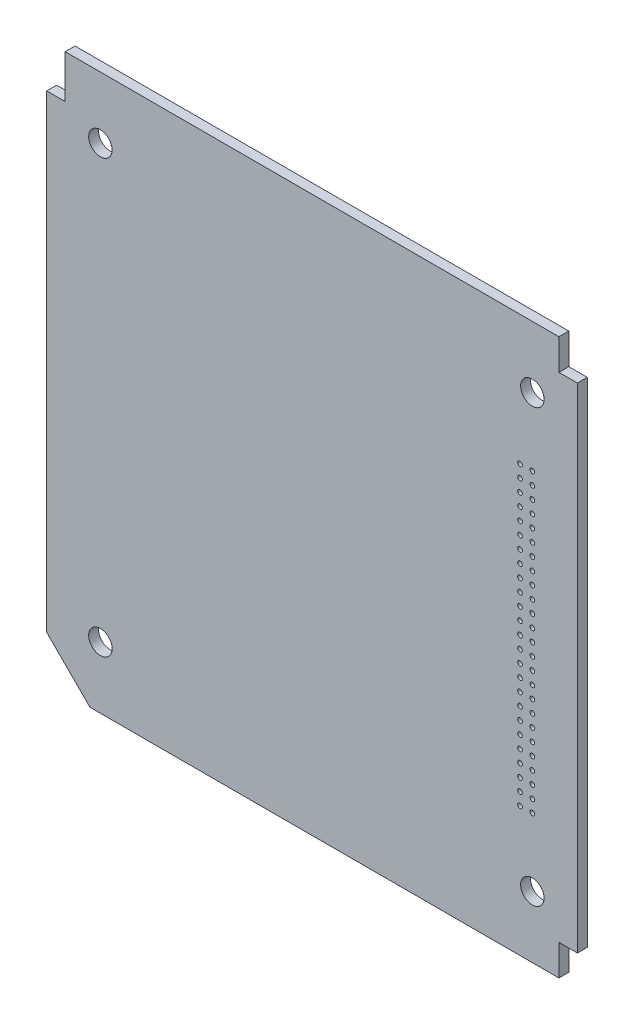
SolidWorks part; units mm, degrees
material "電力回路基板"
ref_plane "正面" through (0, 0, 0) normal (0, 0, 1) x (1, 0, 0)
ref_plane "平面" through (0, 0, 0) normal (0, 1, 0) x (1, 0, 0)
ref_plane "右側面" through (0, 0, 0) normal (1, 0, 0) x (0, 0, -1)
sketch "Sketch1" plane through (0, 0, 0) normal (0, 0, 1) x (1, 0, 0)
  line L0 (-3, 0) -> (-86, 0)
  line L4 (-86, 0) -> (-86, -90)
  line L7 (0, -5) -> (-3, -5)
  line L8 (-3, 0) -> (-3, -5)
  line L11 (0, -85) -> (-3, -85)
  line L12 (-3, -90) -> (-3, -85)
  line L13 (0, -5) -> (0, -85)
  line L14 (-3, -90) -> (-86, -90)
  circle A0 centre (-7.3, -10) radius 1.9
  circle A1 centre (-77.3, -10) radius 1.9
  circle A2 centre (-77.3, -80) radius 1.9
  circle A3 centre (-7.3, -80) radius 1.9
  circle A4 centre (-9.3, -69) radius 0.375
  circle A5 centre (-7.3, -69) radius 0.375
  circle A6 centre (-7.3, -67) radius 0.375
  circle A7 centre (-9.3, -67) radius 0.375
  circle A8 centre (-9.3, -65) radius 0.375
  circle A9 centre (-7.3, -65) radius 0.375
  circle A10 centre (-7.3, -63) radius 0.375
  circle A11 centre (-9.3, -63) radius 0.3838
  circle A12 centre (-9.3, -61) radius 0.375
  circle A13 centre (-7.3, -61) radius 0.375
  circle A14 centre (-7.3, -59) radius 0.375
  circle A15 centre (-9.3, -59) radius 0.375
  circle A16 centre (-7.3, -57) radius 0.375
  circle A17 centre (-9.3, -57) radius 0.375
  circle A18 centre (-9.3, -55) radius 0.375
  circle A19 centre (-7.3, -55) radius 0.375
  circle A20 centre (-7.3, -53) radius 0.375
  circle A21 centre (-9.3, -53) radius 0.375
  circle A22 centre (-9.3, -51) radius 0.375
  circle A23 centre (-7.3, -51) radius 0.375
  circle A24 centre (-7.3, -49) radius 0.375
  circle A25 centre (-9.3, -49) radius 0.375
  circle A26 centre (-9.3, -47) radius 0.375
  circle A27 centre (-7.3, -47) radius 0.375
  circle A28 centre (-7.3, -45) radius 0.375
  circle A29 centre (-9.3, -45) radius 0.3842
  circle A30 centre (-9.3, -43) radius 0.375
  circle A31 centre (-7.3, -43) radius 0.3808
  circle A32 centre (-7.3, -41) radius 0.3774
  circle A33 centre (-9.3, -41) radius 0.3774
  circle A34 centre (-9.3, -39) radius 0.375
  circle A35 centre (-7.3, -39) radius 0.375
  circle A36 centre (-7.3, -37) radius 0.375
  circle A37 centre (-9.3, -37) radius 0.3808
  circle A38 centre (-7.3, -35) radius 0.375
  circle A39 centre (-9.3, -35) radius 0.375
  circle A40 centre (-9.3, -33) radius 0.375
  circle A41 centre (-7.3, -33) radius 0.375
  circle A42 centre (-7.3, -31) radius 0.375
  circle A43 centre (-9.3, -31) radius 0.375
  circle A44 centre (-7.3, -29) radius 0.375
  circle A45 centre (-9.3, -29) radius 0.375
  circle A46 centre (-9.3, -27) radius 0.375
  circle A47 centre (-7.3, -27) radius 0.375
  circle A48 centre (-7.3, -25) radius 0.375
  circle A49 centre (-9.3, -25) radius 0.375
  circle A50 centre (-7.3, -23) radius 0.375
  circle A51 centre (-9.3, -23) radius 0.375
  circle A52 centre (-9.3, -21) radius 0.375
  circle A53 centre (-7.3, -21) radius 0.375
  dimension "D5" = 70
  dimension "D6" = 3
  dimension "D3" = 3.8
  dimension "D10" = 7.3
  dimension "D14" = 10
  dimension "D15" = 10
  dimension "D2" = 90
  dimension "D4" = 70
  dimension "D7" = 5
  dimension "D8" = 86
  dimension "D9" = 7.3
  dimension "D11" = 3
  dimension "D12" = 5
  dimension "D13" = 9.3
  dimension "D16" = 21
extrude "Boss-Extrude1" add sketch "Sketch1" along normal blind 1.6
sketch "ｽｹｯﾁ1" plane through (0, 0, 1.6) normal (0, 0, 1) x (1, 0, 0)
  line L0 (-86, -90) -> (-86, -83)
  line L1 (-86, -83) -> (-79, -90)
  line L2 (-79, -90) -> (-86, -90)
  line L3 (-86, 0) -> (-83, 0)
  line L4 (-83, 0) -> (-83, -7)
  line L5 (-83, -7) -> (-86, -7)
  line L6 (-86, -7) -> (-86, 0)
extrude "ｶｯﾄ - 押し出し1" cut sketch "ｽｹｯﾁ1" against normal blind 10
